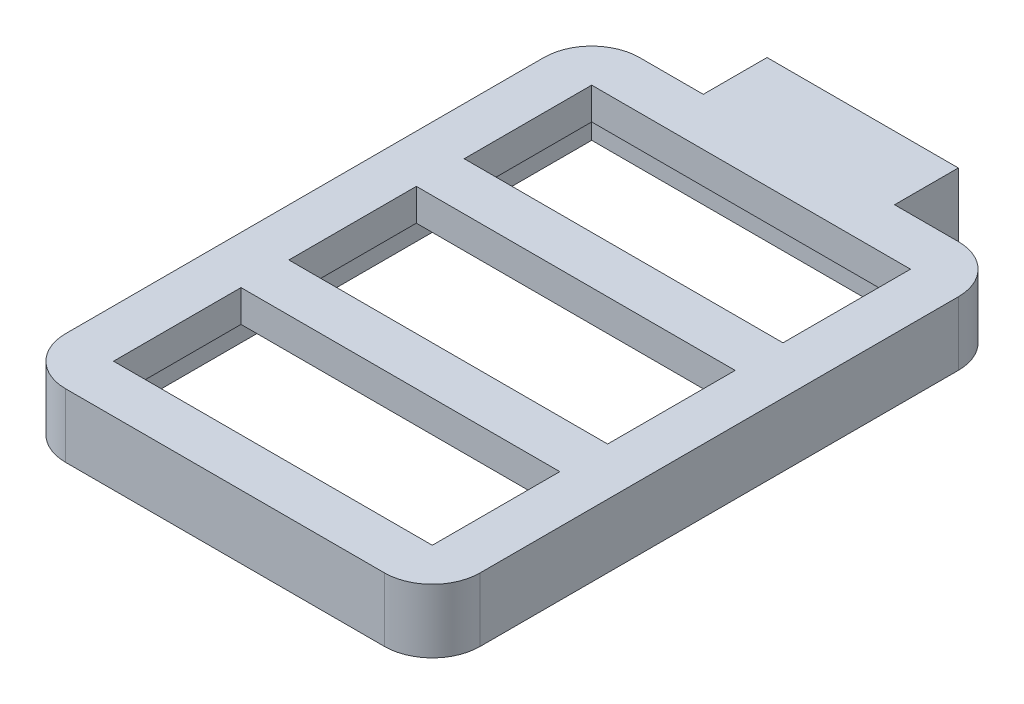
SolidWorks part; units mm, degrees
ref_plane "정면" through (0, 0, 0) normal (0, 0, 1) x (1, 0, 0)
ref_plane "윗면" through (0, 0, 0) normal (0, 1, 0) x (1, 0, 0)
ref_plane "우측면" through (0, 0, 0) normal (1, 0, 0) x (0, 0, -1)
sketch "스케치1" plane through (0, 0, 0) normal (0, 1, 0) x (1, 0, 0)
  line L0 (-65, 90) -> (-65, -90)
  line L1 (-65, -90) -> (65, -90)
  line L2 (65, -90) -> (65, 90)
  line L3 (65, 90) -> (30, 90)
  line L4 (30, 90) -> (30, 110)
  line L5 (30, 110) -> (-30, 110)
  line L6 (-30, 110) -> (-30, 90)
  line L7 (-30, 90) -> (-65, 90)
  dimension "D1" = 180
  dimension "D2" = 180
  dimension "D3" = 130
  dimension "D4" = 90
  dimension "D5" = 35
  dimension "D6" = 35
  dimension "D7" = 20
  dimension "D8" = 65
  dimension "D9" = 90
extrude "보스-돌출1" add sketch "스케치1" along normal blind 20 contours L5 L6 L7 L0 L1 L2 L3 L4
sketch "스케치2" plane through (0, 20, 0) normal (0, 1, 0) x (1, 0, 0)
  line L0 (0, 110) -> (0, -90) construction
  line L1 (30, 110) -> (-30, 110) construction
  line L2 (-65, -90) -> (65, -90) construction
  line L3 (65, 90) -> (30, 90) construction
  line L4 (-50, 75) -> (50, 75)
  line L5 (-50, 75) -> (-50, 35)
  line L6 (-50, 35) -> (50, 35)
  line L7 (50, 75) -> (50, 35)
  line L8 (-50, 75) -> (50, 35) construction
  line L9 (-50, 35) -> (50, 75) construction
  line L10 (-50, 20) -> (50, 20)
  line L11 (-50, 20) -> (-50, -20)
  line L12 (-50, -20) -> (50, -20)
  line L13 (50, 20) -> (50, -20)
  line L14 (-50, 20) -> (50, -20) construction
  line L15 (-50, -20) -> (50, 20) construction
  line L16 (-50, -35) -> (50, -35)
  line L17 (-50, -35) -> (-50, -75)
  line L18 (-50, -75) -> (50, -75)
  line L19 (50, -35) -> (50, -75)
  line L20 (-50, -35) -> (50, -75) construction
  line L21 (-50, -75) -> (50, -35) construction
  point P6 (0, 55)
  point P11 (0, 0)
  point P16 (0, -55)
  dimension "D1" = 100
  dimension "D2" = 100
  dimension "D3" = 100
  dimension "D4" = 40
  dimension "D5" = 40
  dimension "D6" = 40
  dimension "D7" = 15
  dimension "D8" = 15
  dimension "D9" = 15
extrude "컷-돌출1" cut sketch "스케치2" against normal blind 20 contours L19 L16 L17 L18 | L4 L7 L6 L5 | L10 L13 L12 L11
fillet "필렛1" radius 15 4 edges at (-65, 10, 90) (65, 10, 90) (65, 10, -90) (-65, 10, -90)
sketch "스케치3" plane through (0, 0, 0) normal (0, -1, 0) x (1, 0, 0)
  line L1 (-55, 80) -> (55, 80)
  line L2 (-55, 80) -> (-55, -80)
  line L3 (-55, -80) -> (55, -80)
  line L4 (55, 80) -> (55, -80)
  line L5 (-55, 80) -> (55, -80) construction
  line L6 (-55, -80) -> (55, 80) construction
  point P0 (0, 0)
  dimension "D1" = 110
  dimension "D2" = 160
extrude "컷-돌출2" cut sketch "스케치3" against normal blind 10
